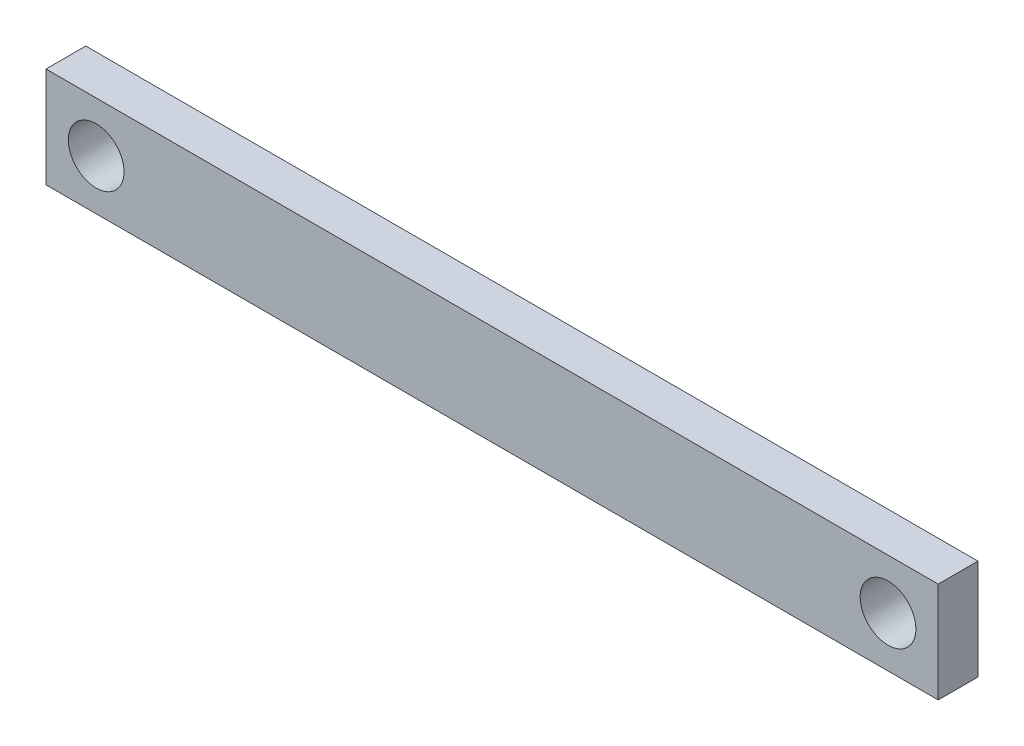
SolidWorks part; units mm, degrees
material "3003 Alloy"
ref_plane "Front Plane" through (0, 0, 0) normal (0, 0, 1) x (1, 0, 0)
ref_plane "Top Plane" through (0, 0, 0) normal (0, 1, 0) x (1, 0, 0)
ref_plane "Right Plane" through (0, 0, 0) normal (1, 0, 0) x (0, 0, -1)
sketch "Sketch1" plane through (0, 0, 0) normal (0, 0, 1) x (1, 0, 0)
  line L0 (0, 3.203) -> (0, -3.203)
  line L1 (-28.481, -3.203) -> (28.481, -3.203)
  line L2 (-28.481, -3.203) -> (-28.481, 3.203)
  line L3 (-28.481, 3.203) -> (28.481, 3.203)
  line L4 (28.481, -3.203) -> (28.481, 3.203)
  line L5 (-28.481, 0) -> (28.481, 0) construction
  circle A0 centre (-25.278, 0) radius 1.778
  circle A1 centre (25.278, 0) radius 1.778
  point P0 (0, 0)
  dimension "D3" = 3.556
  dimension "D4" = 3.203
  dimension "D1" = 25.278
  dimension "D2" = 3.203
extrude "Spreader" add sketch "Sketch1" along normal blind 2.54 contours L2 L5 A0 L0 L3 | L5 L2 L1 L0 A0 | L5 L0 L1 L4 A1 | L0 L5 A1 L4 L3
sketch "Sketch2" plane through (0, 0, 0) normal (0, 0, -1) x (-1, 0, 0)
  circle A0 centre (25.278, 0) radius 2.3241
  circle A1 centre (-25.278, 0) radius 2.3241
  circle A2 centre (25.278, 0) radius 1.778 construction
  circle A3 centre (-25.278, 0) radius 1.778 construction
  circle A4 centre (25.278, 0) radius 1.778
  circle A5 centre (-25.278, 0) radius 1.778
  dimension "D1" = 4.6482
  dimension "D2" = 4.6482
sketch "Sketch3" plane through (0, 0, 2.54) normal (0, 0, 1) x (1, 0, 0)
  line L0 (-28.481, -3.203) -> (28.481, -3.203) construction
  line L1 (-22.5, 3.203) -> (22.5, 3.203)
  line L2 (-22.5, 3.203) -> (-22.5, -3.203)
  line L3 (-22.5, -3.203) -> (22.5, -3.203)
  line L4 (22.5, 3.203) -> (22.5, -3.203)
  line L5 (-22.5, 3.203) -> (22.5, -3.203) construction
  line L6 (-22.5, -3.203) -> (22.5, 3.203) construction
  point P0 (0, 0)
  dimension "D1" = 45
split line "Socket Heads" [suppressed]
split line "Cell Tabs" [suppressed]
equation "\"D1@Sketch1\"=22.5mm + \"D3@Sketch1\"/2+1mm"
equation "\"D4@Sketch1\"=1.425mm + \"D3@Sketch1\"/2"
equation "\"D2@Sketch1\"=1.425mm+\"D3@Sketch1\"/2"
